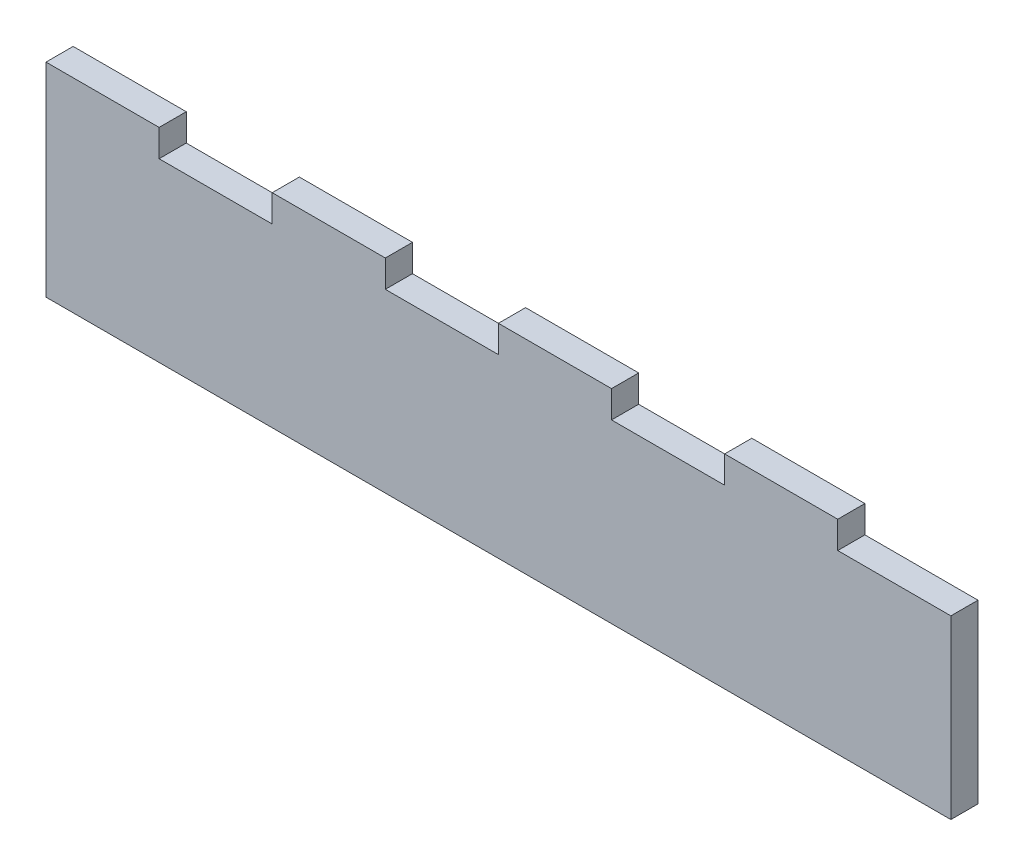
SolidWorks part; units mm, degrees
ref_plane "Plano frontal" through (0, 0, 0) normal (0, 0, 1) x (1, 0, 0)
ref_plane "Plano superior" through (0, 0, 0) normal (0, 1, 0) x (1, 0, 0)
ref_plane "Plano direito" through (0, 0, 0) normal (1, 0, 0) x (0, 0, -1)
sketch "Esboço1" plane through (0, 0, 0) normal (0, 0, 1) x (1, 0, 0)
  line L0 (50, 39) -> (50, 45)
  line L1 (0, 0) -> (200, 0)
  line L2 (0, 0) -> (0, 39)
  line L3 (25, 39) -> (50, 39)
  line L4 (200, 0) -> (200, 39)
  line L6 (0, 39) -> (0, 45)
  line L7 (0, 45) -> (25, 45)
  line L8 (25, 39) -> (25, 45)
  line L10 (75, 39) -> (75, 45)
  line L11 (50, 45) -> (75, 45)
  line L12 (100, 39) -> (100, 45)
  line L14 (125, 39) -> (125, 45)
  line L15 (100, 45) -> (125, 45)
  line L16 (150, 39) -> (150, 45)
  line L18 (175, 39) -> (175, 45)
  line L19 (150, 45) -> (175, 45)
  line L20 (75, 39) -> (100, 39)
  line L21 (125, 39) -> (150, 39)
  line L22 (175, 39) -> (200, 39)
  dimension "D1" = 39
  dimension "D2" = 200
  dimension "D3" = 6
  dimension "D4" = 25
  dimension "D5" = 4
extrude "Ressalto-extrusão1" add sketch "Esboço1" along normal blind 6
